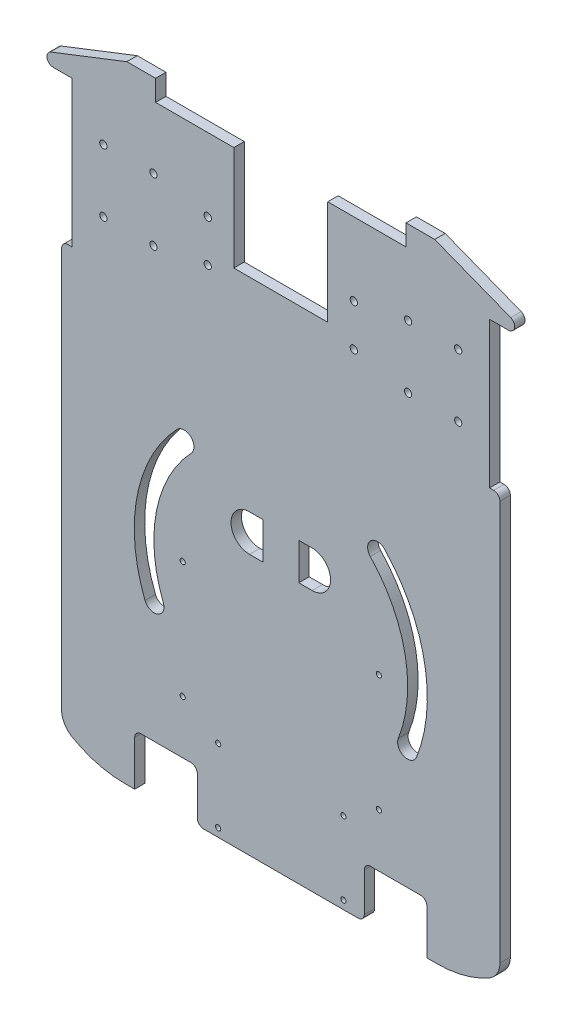
SolidWorks part; units mm, degrees
ref_plane "前视基准面" through (0, 0, 0) normal (0, 0, 1) x (1, 0, 0)
ref_plane "上视基准面" through (0, 0, 0) normal (0, 1, 0) x (1, 0, 0)
ref_plane "右视基准面" through (0, 0, 0) normal (1, 0, 0) x (0, 0, -1)
sketch "草图1" plane through (0, 0, 0) normal (0, 0, 1) x (1, 0, 0)
  line L1 (-150, 150) -> (150, 150)
  line L2 (-150, 150) -> (-150, -150)
  line L3 (-150, -150) -> (150, -150)
  line L4 (150, 150) -> (150, -150)
  line L5 (-150, 150) -> (150, -150) construction
  line L6 (-150, -150) -> (150, 150) construction
  point P0 (0, 0)
  dimension "D1" = 300
  dimension "D2" = 300
extrude "凸台-拉伸2" add sketch "草图1" along normal blind 5
sketch "草图4" plane through (0, 0, 5) normal (0, 0, 1) x (1, 0, 0)
  line L0 (-22.5, 150) -> (-22.5, 90)
  line L1 (150, 150) -> (-150, 150) construction
  line L2 (-22.5, 90) -> (22.5, 90)
  line L3 (22.5, 90) -> (22.5, 150)
  line L4 (0, 161.4477) -> (0, -168.0628) construction
  line L5 (22.5, 150) -> (-22.5, 150)
  dimension "D1" = 45
  dimension "D2" = 60
extrude "切除-拉伸3" cut sketch "草图4" against normal blind 5
sketch "草图5" plane through (0, 0, 5) normal (0, 0, 1) x (1, 0, 0)
  line L2 (-125, 150) -> (125, 150)
  line L3 (-125, 150) -> (-125, -150)
  line L4 (-125, -150) -> (125, -150)
  line L5 (125, 150) -> (125, -150)
  line L6 (-125, 150) -> (125, -150) construction
  line L7 (-125, -150) -> (125, 150) construction
  line L8 (-150, -150) -> (150, -150) construction
  point P2 (0, 0)
  dimension "D1" = 300
  dimension "D2" = 250
extrude "切除-拉伸4" cut sketch "草图5" against normal blind 5 flip side to cut
sketch "草图6" plane through (0, 0, 5) normal (0, 0, 1) x (1, 0, 0)
  line L0 (-22.5, 150) -> (-125, 150) construction
  line L1 (-125, 150) -> (-125, -150) construction
  line L2 (0, -197.0335) -> (0, 263.7376) construction
  line L3 (-125, -150) -> (125, -150) construction
  circle A0 centre (-85, 110) radius 1.75
  circle A1 centre (-61, 110) radius 1.75
  circle A2 centre (-61, 80) radius 1.75
  circle A3 centre (-85, 80) radius 1.75
  circle A4 centre (85, 80) radius 1.75
  circle A5 centre (61, 80) radius 1.75
  circle A6 centre (61, 110) radius 1.75
  circle A7 centre (85, 110) radius 1.75
  circle A8 centre (-47, -100) radius 1.25
  circle A9 centre (-47, -44) radius 1.25
  circle A10 centre (47, -44) radius 1.25
  circle A11 centre (47, -100) radius 1.25
  circle A12 centre (-35, 105) radius 1.75
  circle A13 centre (-35, 85) radius 1.75
  circle A14 centre (35, 85) radius 1.75
  circle A15 centre (35, 105) radius 1.75
  dimension "D1" = 3.5
  dimension "D8" = 2.5
  dimension "D10" = 2.5
  dimension "D13" = 3.5
  dimension "D15" = 3.5
  dimension "D2" = 40
  dimension "D3" = 40
  dimension "D6" = 30
  dimension "D7" = 24
  dimension "D9" = 94
  dimension "D11" = 56
  dimension "D12" = 50
  dimension "D14" = 70
  dimension "D16" = 20
  dimension "D17" = 45
  dimension "D4" = 2
  dimension "D5" = 2
extrude "切除-拉伸5" cut sketch "草图6" against normal blind 5
sketch "草图7" plane through (0, 0, 5) normal (0, 0, 1) x (1, 0, 0)
  line L0 (-125, 150) -> (-125, -150) construction
  line L1 (-150, 60) -> (-100, 60)
  line L2 (-150, 60) -> (-150, 130)
  line L3 (-150, 130) -> (-100, 130)
  line L4 (-100, 60) -> (-100, 130)
  line L5 (-150, 60) -> (-100, 130) construction
  line L6 (-150, 130) -> (-100, 60) construction
  line L7 (-85, 110) -> (-85, 80) construction
  line L8 (0, 0) -> (0, 158.3194) construction
  line L9 (150, 130) -> (100, 60) construction
  line L10 (150, 60) -> (100, 130) construction
  line L11 (100, 60) -> (100, 130)
  line L12 (150, 130) -> (100, 130)
  line L13 (150, 60) -> (150, 130)
  line L14 (150, 60) -> (100, 60)
  point P0 (-125, 95)
  point P11 (-85, 95)
  point P19 (125, 95)
  dimension "D1" = 70
  dimension "D2" = 50
extrude "切除-拉伸6" cut sketch "草图7" against normal blind 10
sketch "草图8" plane through (0, 0, 5) normal (0, 0, 1) x (1, 0, 0)
  line L0 (-125, 130) -> (-73.75, 150)
  line L1 (-22.5, 150) -> (-125, 150) construction
  line L2 (0, -3.4074) -> (0, 158.1434) construction
  line L7 (125, 130) -> (73.75, 150)
  line L8 (-125, 60) -> (-125, -150) construction
  line L9 (-125, -150) -> (125, -150) construction
  line L10 (75, -150) -> (125, -150)
  line L11 (-125, 130) -> (-125, 150)
  line L12 (-125, 150) -> (-73.75, 150)
  line L13 (73.75, 150) -> (125, 150)
  line L14 (125, 150) -> (125, 130)
  line L15 (-70, -125.5051) -> (-70, -150)
  line L16 (-70, -125.5051) -> (-40, -125.5051)
  line L17 (70, -125.5051) -> (70, -150)
  line L18 (-70, -150) -> (-40, -150)
  line L20 (-60, 150) -> (-60, 140)
  line L21 (-60, 140) -> (60, 140)
  line L22 (60, 140) -> (60, 150)
  line L23 (125, 150) -> (22.5, 150) construction
  line L24 (60, 150) -> (-60, 150)
  line L25 (-105, 60) -> (-105, -134.641)
  line L26 (-100, 60) -> (-125, 60)
  line L27 (-125, 60) -> (-125, -150)
  line L28 (-125, -150) -> (125, -150)
  line L29 (125, -150) -> (125, 60)
  line L30 (125, 60) -> (100, 60)
  line L31 (100, 60) -> (100, 130)
  line L32 (100, 130) -> (125, 130)
  line L33 (125, 130) -> (125, 150)
  line L34 (125, 150) -> (22.5, 150)
  line L35 (22.5, 150) -> (22.5, 90)
  line L36 (22.5, 90) -> (-22.5, 90)
  line L37 (-22.5, 90) -> (-22.5, 150)
  line L38 (-22.5, 150) -> (-125, 150)
  line L39 (-125, 150) -> (-125, 130)
  line L40 (-125, 130) -> (-100, 130)
  line L41 (-100, 130) -> (-100, 60)
  line L42 (-125, 60) -> (-100, 60) construction
  line L43 (-125, 60) -> (-125, -150)
  line L44 (-125, -150) -> (-75, -150)
  line L46 (-105, 60) -> (-125, 60)
  line L48 (-40, -125.5051) -> (-40, -150)
  line L49 (125, 60) -> (125, -150)
  line L50 (105, 60) -> (105, -134.641)
  line L51 (105, 60) -> (125, 60)
  line L52 (40, -125.5051) -> (40, -150)
  line L53 (40, -125.5051) -> (70, -125.5051)
  line L54 (40, -150) -> (70, -150)
  line L55 (-15.0326, -16.2353) -> (-8.6187, -16.2353) construction
  line L58 (-15.0326, -7.4161) -> (-8.6187, -7.4161)
  line L59 (-15.0326, -25.0544) -> (-8.6187, -25.0544)
  line L60 (8.6187, -25.0544) -> (15.0326, -25.0544)
  line L62 (-8.6187, -7.4161) -> (-8.6187, -25.0544)
  line L64 (8.6187, -7.4161) -> (8.6187, -25.0544)
  line L67 (8.6187, -16.2353) -> (15.0326, -16.2353) construction
  line L68 (8.6187, -7.4161) -> (15.0326, -7.4161)
  arc A0 (-100, -143.3013) -> (-75, -150) centre (-75, -100) ccw
  arc A1 (100, -143.3013) -> (75, -150) centre (75, -100) cw
  arc A2 (-100, -143.3013) -> (-105, -134.641) centre (-95, -134.641) cw
  arc A3 (100, -143.3013) -> (105, -134.641) centre (95, -134.641) ccw
  arc A4 (-60.6754, -67.4724) -> (-46.3006, 6.2135) centre (4.4173, -41.9258) cw construction
  arc A5 (-49.7068, 9.4466) -> (-65.0471, -69.1882) centre (4.4173, -41.9258) ccw
  arc A6 (-42.8943, 2.9804) -> (-56.3037, -65.7567) centre (4.4173, -41.9258) ccw
  arc A7 (-42.8943, 2.9804) -> (-49.7068, 9.4466) centre (-46.3006, 6.2135) ccw
  arc A8 (-65.0471, -69.1882) -> (-56.3037, -65.7567) centre (-60.6754, -67.4724) ccw
  arc A9 (60.6754, -67.4724) -> (46.3006, 6.2135) centre (-4.4173, -41.9258) ccw construction
  arc A10 (49.7068, 9.4466) -> (65.0471, -69.1882) centre (-4.4173, -41.9258) cw
  arc A11 (42.8943, 2.9804) -> (56.3037, -65.7567) centre (-4.4173, -41.9258) cw
  arc A12 (42.8943, 2.9804) -> (49.7068, 9.4466) centre (46.3006, 6.2135) cw
  arc A13 (65.0471, -69.1882) -> (56.3037, -65.7567) centre (60.6754, -67.4724) cw
  arc A16 (-15.0326, -7.4161) -> (-15.0326, -25.0544) centre (-15.0326, -16.2353) ccw
  arc A17 (15.0326, -25.0544) -> (15.0326, -7.4161) centre (15.0326, -16.2353) ccw
  point P27 (0, -125.5051)
  point P65 (-64.2152, -28.5368)
  point P73 (64.2152, -28.5368)
  point P80 (0, -16.2353)
  point P92 (0, -16.2353)
  dimension "D1" = 50
  dimension "D8" = 10
  dimension "D3" = 25
  dimension "D4" = 5
  dimension "D5" = 10
  dimension "D6" = 60
  dimension "D7" = 20
  dimension "D9" = 140
  dimension "D10" = 80
  dimension "D2" = 0
extrude "切除-拉伸7" cut sketch "草图8" against normal blind 10
fillet "圆角1" radius 3 10 edges at (125, 130, 2.5) (-125, 130, 2.5) (70, -125.5051, 2.5) (40, -125.5051, 2.5) (-40, -125.5051, 2.5) (-70, -125.5051, 2.5) (40, -150, 2.5) (-40, -150, 2.5) (105, 60, 2.5) (-105, 60, 2.5)
hole_wizard "M3 螺纹孔1" positions "草图9" profile "草图10" tap size "M3" standard "GB"
sketch "草图9" plane through (0, 0, 5) normal (0, 0, 1) x (1, 0, 0)
  line L0 (-40, -147) -> (-40, -128.5051) construction
  line L1 (-40, -150) -> (40, -150) construction
  point P0 (-30, -146)
  point P15 (30, -146)
  point P16 (30, -111)
  point P17 (-30, -111)
  dimension "D1" = 10
  dimension "D2" = 4
  dimension "D5" = 35
  dimension "D3" = 2
  dimension "D4" = 2
sketch "草图10" plane through (-30, -146, 5) normal (1, 0, 0) x (0, -1, 0)
  line L0 (0, 0) -> (0, 10.7511)
  line L1 (0, 10.7511) -> (1.25, 10)
  line L2 (1.25, 10) -> (1.25, 0)
  line L5 (1.25, 0) -> (0, 0)
  line L10 (0, 10.7511) -> (-1.25, 10) construction
  line L11 (0, -6.35) -> (0, 107.95) construction
  dimension "螺纹孔钻头直径" = 2.5
  dimension "螺纹孔钻头深度" = 10
  dimension "导头角度" = 118
cosmetic thread "孔螺蚊线1" parameters "D1"=5, "D2"=3
cosmetic thread "孔螺蚊线2" parameters "D1"=5, "D2"=3
cosmetic thread "孔螺蚊线3" parameters "D1"=5, "D2"=3
cosmetic thread "孔螺蚊线4" parameters "D1"=5, "D2"=3
